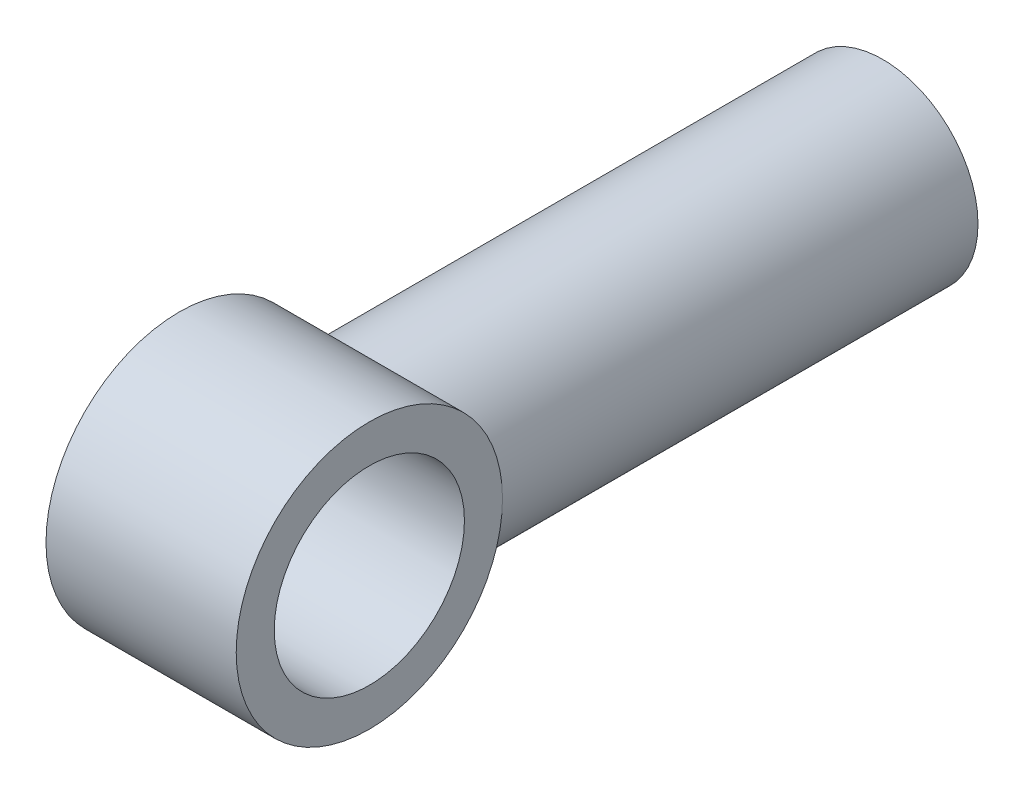
SolidWorks part; units mm, degrees
ref_plane "Front Plane" through (0, 0, 0) normal (0, 0, 1) x (1, 0, 0)
ref_plane "Top Plane" through (0, 0, 0) normal (0, 1, 0) x (1, 0, 0)
ref_plane "Right Plane" through (0, 0, 0) normal (1, 0, 0) x (0, 0, -1)
sketch "Sketch2" plane through (0, 0, 0) normal (0, 0, 1) x (1, 0, 0)
  circle A0 centre (0, 0) radius 3.175
  dimension "D1" = 6.35
extrude "Boss-Extrude1" add sketch "Sketch2" against normal blind 20.32
sketch "Sketch3" plane through (0, 0, 0) normal (1, 0, 0) x (0, 0, -1)
  circle A0 centre (0, 0) radius 4.445
  dimension "D1" = 8.89
extrude "Boss-Extrude2" add sketch "Sketch3" along normal mid plane 6.35
sketch "Sketch4" plane through (3.175, 0, 0) normal (1, 0, 0) x (0, 0, -1)
  circle A0 centre (0, 0) radius 3.175
  dimension "D1" = 6.35
extrude "Cut-Extrude1" cut sketch "Sketch4" against normal blind 6.35
